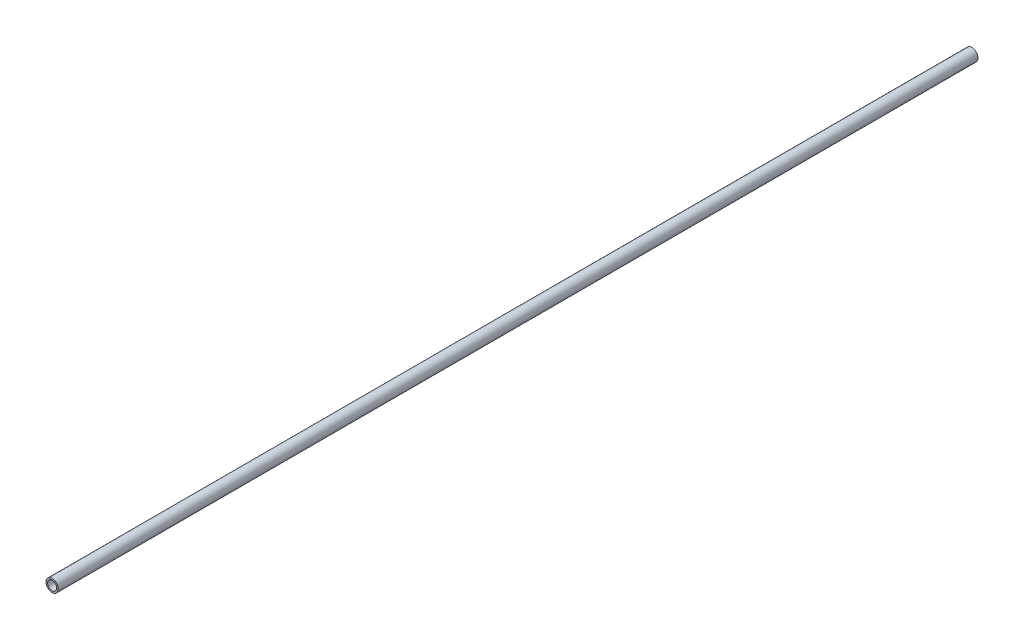
SolidWorks part; units mm, degrees
ref_plane "Front" through (0, 0, 0) normal (0, 0, 1) x (1, 0, 0)
ref_plane "Top" through (0, 0, 0) normal (0, 1, 0) x (1, 0, 0)
ref_plane "Side" through (0, 0, 0) normal (1, 0, 0) x (0, 0, -1)
sketch "PipeSketch" plane through (0, 0, 0) normal (0, 0, 1) x (1, 0, 0)
  circle A0 centre (0, 0) radius 36.576
  circle A1 centre (0, 0) radius 27.051
  dimension "OuterDiameter" = 73.152
  dimension "InnerDiameter" = 54.102
extrude "Extrusion" add sketch "PipeSketch" along normal blind 5486.4
sketch "FilterSketch" plane through (0, 0, 0) normal (0, 0, 1) x (1, 0, 0)
  circle A0 centre (0, 0) radius 31.75 construction
  dimension "NominalDiameter" = 63.5
